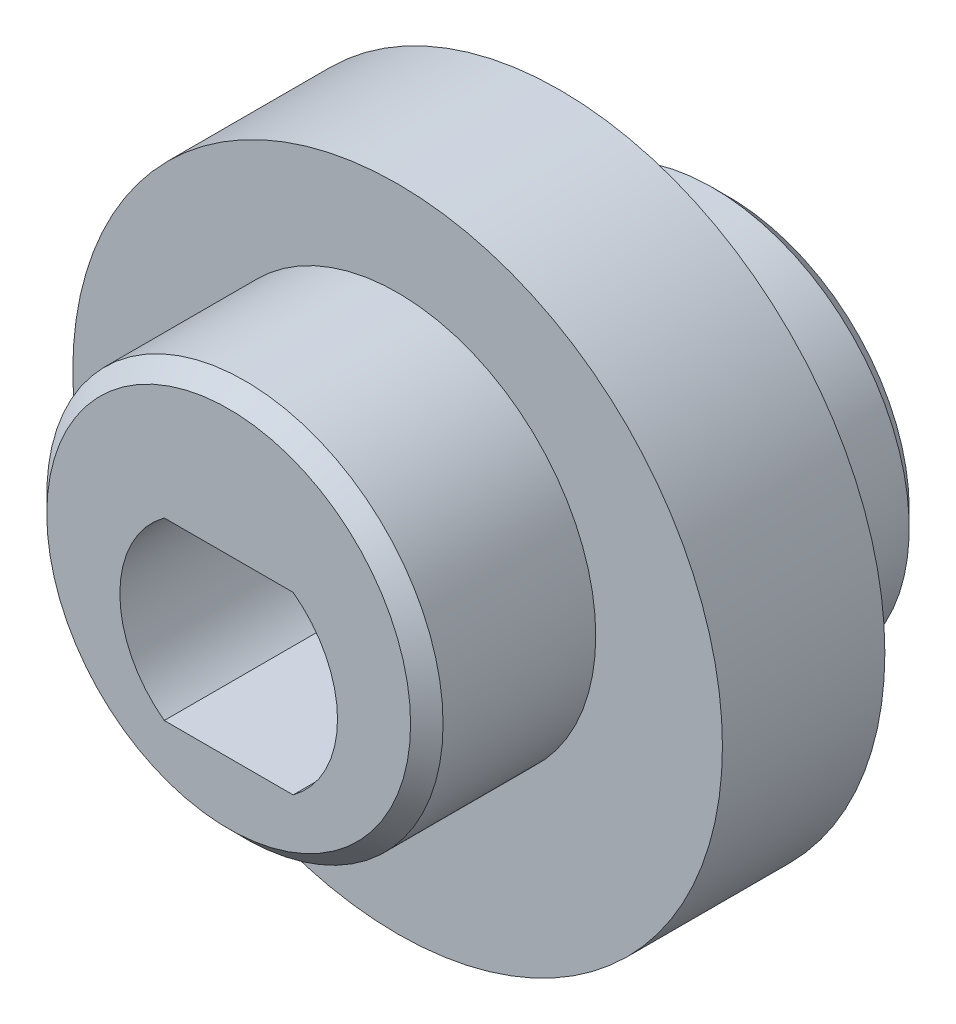
SolidWorks part; units mm, degrees
material "Polylactic Acid (PLA)"
ref_plane "Front Plane" through (0, 0, 0) normal (0, 0, 1) x (1, 0, 0)
ref_plane "Top Plane" through (0, 0, 0) normal (0, 1, 0) x (1, 0, 0)
ref_plane "Right Plane" through (0, 0, 0) normal (1, 0, 0) x (0, 0, -1)
sketch "Sketch6" plane through (0, 0, 0) normal (0, 0, 1) x (1, 0, 0)
  circle A0 centre (0, 0) radius 6
  dimension "D1" = 12
extrude "Boss-Extrude4" add sketch "Sketch6" along normal mid plane 5
sketch "Sketch7" plane through (0, 0, 2.5) normal (0, 0, 1) x (1, 0, 0)
  circle A0 centre (0, 1) radius 6.1
  dimension "D1" = 12.2
  dimension "D2" = 1
extrude "Boss-Extrude5" add sketch "Sketch7" along normal blind 5.2
sketch "Sketch8" plane through (0, 0, -2.5) normal (0, 0, -1) x (-1, 0, 0)
  circle A0 centre (0, -1) radius 6.05
  dimension "D1" = 12.1
  dimension "D2" = 1
extrude "Boss-Extrude6" add sketch "Sketch8" along normal blind 5.2
sketch "Sketch13" plane through (0, 0, 2.5) normal (0, 0, 1) x (1, 0, 0)
  circle A2 centre (0, 0) radius 10
  dimension "D1" = 20
extrude "Boss-Extrude7" add sketch "Sketch13" against normal up to surface (5 mm away) up to face at (0, 5.525, -2.5)
sketch "Sketch11" plane through (0, 0, 2.5) normal (0, 0, 1) x (1, 0, 0)
  line L0 (-1.9831, -2.7) -> (1.9831, -2.7)
  line L1 (-1.9164, -2.5) -> (1.9164, -2.5) construction
  line L2 (-1.9164, -2.5) -> (-1.9164, 2.5) construction
  line L3 (-1.9164, 2.5) -> (1.9164, 2.5) construction
  line L4 (1.9164, -2.5) -> (1.9164, 2.5) construction
  line L5 (-1.9164, -2.5) -> (1.9164, 2.5) construction
  line L6 (-1.9164, 2.5) -> (1.9164, -2.5) construction
  line L7 (-1.9831, 2.7) -> (1.9831, 2.7)
  arc A0 (-1.9164, 2.5) -> (-1.9164, -2.5) centre (0, 0) ccw construction
  arc A1 (1.9164, -2.5) -> (1.9164, 2.5) centre (0, 0) ccw construction
  arc A2 (1.9831, -2.7) -> (1.9831, 2.7) centre (0, 0) ccw
  arc A3 (-1.9831, 2.7) -> (-1.9831, -2.7) centre (0, 0) ccw
  dimension "D1" = 6.3
  dimension "D2" = 2.5
  dimension "D3" = 0.2
extrude "Cut-Extrude1" cut sketch "Sketch11" against normal through all both and the other way through all
chamfer "Chamfer1" distance 0.5 angle 45 2 edges at (-6.05, -1, -7.7) (6.1, 1, 7.7)
